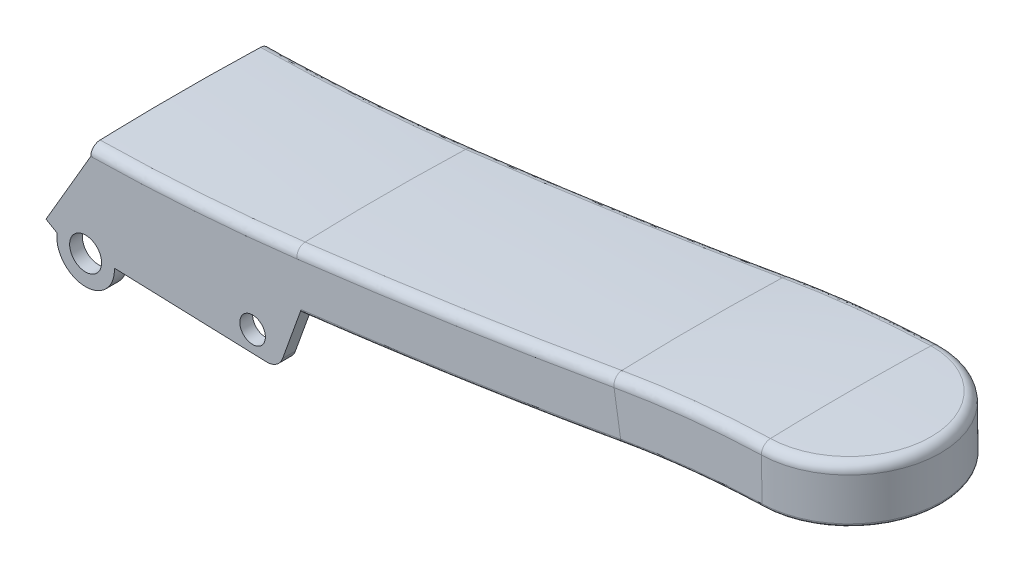
SolidWorks part; units mm, degrees
material "Ferro fundido cinza (SN)"
ref_plane "Plano frontal" through (0, 0, 0) normal (0, 0, 1) x (1, 0, 0)
ref_plane "Plano superior" through (0, 0, 0) normal (0, 1, 0) x (1, 0, 0)
ref_plane "Plano direito" through (0, 0, 0) normal (1, 0, 0) x (0, 0, -1)
sketch "Esboço1" plane through (0, 0, 0) normal (0, 0, 1) x (1, 0, 0)
  arc A0 (0, 0) -> (33, 2.2682) centre (-5.3127, 318.4885) ccw
  arc A1 (33, 2.2682) -> (83, 9.6978) centre (-79.8486, 933.6841) ccw
  arc A2 (83, 9.6978) -> (105, 12) centre (110.3739, -145.6188) cw
  dimension "D1" = 105
  dimension "D2" = 22
  dimension "D3" = 33
  dimension "D4" = 12
sketch "Esboço2" plane through (0, 0, 0) normal (1, 0, 0) x (0, 0, -1)
  line L0 (-14, 7.4427) -> (-14, 0.8944)
  line L1 (0, 9.1363) -> (0, 8.064) construction
  line L2 (0, 9.6978) -> (0, 2.2682) construction
  line L3 (-13, 6.736) -> (-13, 0.8944)
  line L4 (13, 6.736) -> (13, 0.8944)
  line L5 (14, 7.4427) -> (14, 0.8944)
  arc A0 (12.5464, 8.942) -> (-12.5464, 8.942) centre (0, -396.1075) ccw
  arc A1 (-14, 0.8944) -> (-13, 0.8944) centre (-13.5, 0.8944) ccw
  arc A2 (12.1183, 7.6759) -> (0, 8.064) centre (-0.0267, -182.1722) ccw
  arc A3 (-13, 6.736) -> (-12.1183, 7.6759) centre (-12.0582, 6.736) cw
  arc A4 (-12.1183, 7.6759) -> (0, 8.064) centre (0.0267, -182.1722) cw
  arc A5 (13, 6.736) -> (12.1183, 7.6759) centre (12.0582, 6.736) ccw
  arc A6 (14, 0.8944) -> (13, 0.8944) centre (13.5, 0.8944) cw
  arc A7 (-12.5464, 8.942) -> (-14, 7.4427) centre (-12.5, 7.4427) ccw
  arc A8 (14, 7.4427) -> (12.5464, 8.942) centre (12.5, 7.4427) ccw
  point P34 (-14, 8.8944)
  point P37 (14, 8.8944)
  dimension "D1" = 1.5
  dimension "D3" = 0.5
  dimension "D2" = 8
sweep "Varredura1" add profiles "Esboço2" path "Esboço1"
sketch "Esboço3" plane through (105.177, 1.8304, 0) normal (0.9998, 0.0174, 0) x (0, 0, -1)
  line L0 (0, 19.3074) -> (0, -1.0381) construction
  line L1 (14, 17.6138) -> (14, 11.0655)
  line L2 (13, 11.0655) -> (13, 16.9071)
  line L3 (0, 19.3074) -> (0, 18.2351)
  arc A0 (12.5464, 19.1131) -> (-12.5464, 19.1131) centre (0, -385.9364) ccw construction
  arc A1 (12.5464, 19.1131) -> (14, 17.6138) centre (12.5, 17.6138) cw
  arc A2 (0, 19.3074) -> (12.5464, 19.1131) centre (0, -385.9364) cw
  arc A3 (14, 11.0655) -> (13, 11.0655) centre (13.5, 11.0655) cw
  arc A4 (13, 11.0655) -> (14, 11.0655) centre (13.5, 11.0655) ccw construction
  arc A5 (13, 16.9071) -> (12.1183, 17.847) centre (12.0582, 16.9071) ccw
  arc A6 (12.1183, 17.847) -> (0, 18.2351) centre (-0.0267, -172.0011) ccw
revolve "Revolução1" add sketch "Esboço3" angle 180 about L0
sketch "Esboço6" plane through (0, 0, 14) normal (0, 0, 1) x (1, 0, 0)
  line L0 (0, 7.4427) -> (-7, -4.5573)
  line L1 (-7, -4.5573) -> (-5.2724, -5.565)
  line L2 (3.685, -5.8388) -> (27.4648, -6.6448)
  line L3 (29.9994, -4.9263) -> (32.9072, 3.1577)
  line L4 (32.9072, 3.1577) -> (32.2282, 9.6708)
  arc A0 (-5.2724, -5.565) -> (3.685, -5.8388) centre (-0.8064, -6.1167) ccw
  arc A1 (27.4648, -6.6448) -> (29.9994, -4.9263) centre (27.5528, -4.0463) ccw
  arc A2 (32.2282, 9.6708) -> (0, 7.4427) centre (-5.2091, 316.991) cw
  dimension "D1" = 12
  dimension "D3" = 2.6
  dimension "D5" = 4.5
  dimension "D2" = 2
  dimension "D4" = 18
  dimension "D6" = 7
extrude "Ressalto-extrusão1" add sketch "Esboço6" against normal blind 2
mirror "Espelhar1" about plane through (0, 0, 0) normal (0, 0, 1) of "Ressalto-extrusão1"
sketch "Esboço7" plane through (0, 0, 14) normal (0, 0, 1) x (1, 0, 0)
  circle A0 centre (-0.8064, -6.1167) radius 2.5
  arc A1 (-5.2724, -5.565) -> (3.685, -5.8388) centre (-0.8064, -6.1167) ccw construction
extrude "Corte-extrusão1" cut sketch "Esboço7" against normal through all
sketch "Esboço8" plane through (0, 0, 14) normal (0, 0, 1) x (1, 0, 0)
  line L0 (3.685, -5.8388) -> (27.4648, -6.6448) construction
  circle A0 centre (25.3072, -3.3698) radius 2
  dimension "D1" = 4
  dimension "D2" = 7.6
  dimension "D3" = 3.2
extrude "Corte-extrusão2" cut sketch "Esboço8" against normal through all
